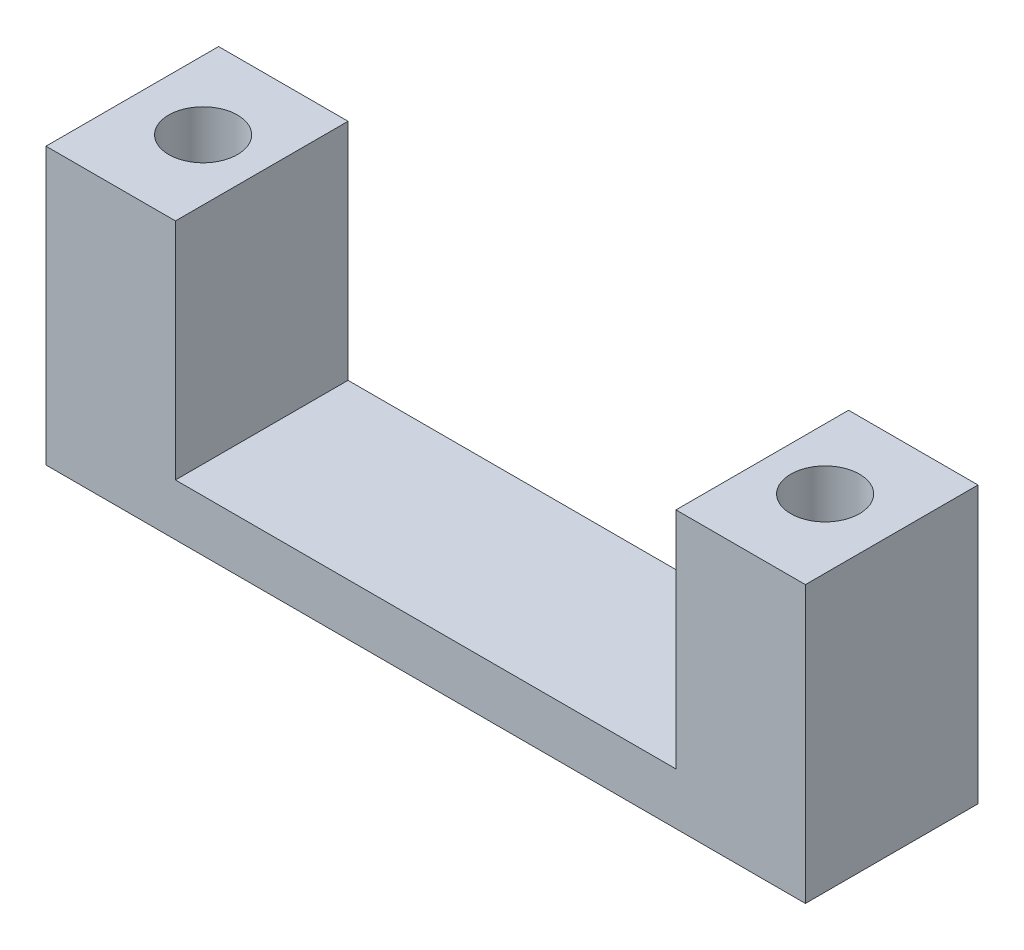
SolidWorks part; units mm, degrees
ref_plane "Front Plane" through (0, 0, 0) normal (0, 0, 1) x (1, 0, 0)
ref_plane "Top Plane" through (0, 0, 0) normal (0, 1, 0) x (1, 0, 0)
ref_plane "Right Plane" through (0, 0, 0) normal (1, 0, 0) x (0, 0, -1)
sketch "Sketch1" plane through (0, 0, 0) normal (0, 1, 0) x (1, 0, 0)
  line L1 (0, 0) -> (-55.88, 0)
  line L2 (0, 0) -> (0, 12.7)
  line L3 (0, 12.7) -> (-55.88, 12.7)
  line L4 (-55.88, 0) -> (-55.88, 12.7)
  dimension "D1" = 55.88
  dimension "D2" = 12.7
extrude "Boss-Extrude1" add sketch "Sketch1" along normal blind 3.81
sketch "Sketch2" plane through (0, 3.81, 0) normal (0, 1, 0) x (1, 0, 0)
  line L0 (-55.88, 0) -> (0, 0) construction
  line L1 (-55.88, 12.7) -> (-46.355, 12.7)
  line L2 (-55.88, 12.7) -> (-55.88, 0)
  line L3 (-55.88, 0) -> (-46.355, 0)
  line L4 (-46.355, 12.7) -> (-46.355, 0)
  line L6 (0, 12.7) -> (-9.525, 12.7)
  line L7 (0, 12.7) -> (0, 0)
  line L8 (0, 0) -> (-9.525, 0)
  line L9 (-9.525, 12.7) -> (-9.525, 0)
  dimension "D1" = 36.83
  dimension "D2" = 9.525
extrude "Boss-Extrude2" add sketch "Sketch2" along normal blind 16.51
hole_wizard "#8 (0.199) Diameter Hole1" positions "Sketch3" profile "Sketch4" hole size "#8" standard "ANSI Inch"
sketch "Sketch3" plane through (0, 20.32, 0) normal (0, 1, 0) x (1, 0, 0)
  line L0 (-55.88, 12.7) -> (-55.88, 0) construction
  line L1 (0, 0) -> (0, 12.7) construction
  point P0 (-50.8254, 6.5052)
  point P2 (-5.0546, 6.5052)
  dimension "D1" = 45.7708
  dimension "D2" = 5.0546
  dimension "D3" = 5.0546
sketch "Sketch4" plane through (-50.8254, 20.32, -6.5052) normal (1, 0, 0) x (0, 0, 1)
  line L0 (0, 0) -> (0, 8.6306)
  line L1 (0, 8.6306) -> (2.5273, 7.112)
  line L2 (2.5273, 7.112) -> (2.5273, 0)
  line L5 (2.5273, 0) -> (0, 0)
  line L10 (0, 8.6306) -> (-2.5273, 7.112) construction
  line L11 (0, -6.35) -> (0, 107.95) construction
  dimension "Hole Dia." = 5.0546
  dimension "Hole Depth" = 7.112
  dimension "Drill Angle" = 118
